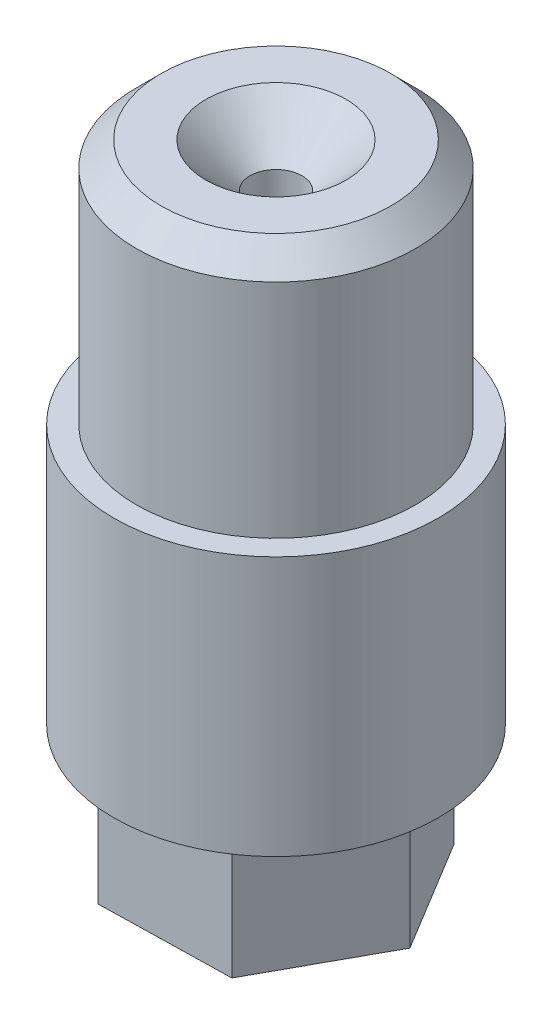
SolidWorks part; units mm, degrees
material "6061-T6 (SS)"
ref_plane "Front Plane" through (0, 0, 0) normal (0, 0, 1) x (1, 0, 0)
ref_plane "Top Plane" through (0, 0, 0) normal (0, 1, 0) x (1, 0, 0)
ref_plane "Right Plane" through (0, 0, 0) normal (1, 0, 0) x (0, 0, -1)
ref_axis "Axis1" through (0, 110.1512, 0) along (0, -1, 0)
sketch "Sketch1" plane through (0, 0, 0) normal (0, 0, 1) x (1, 0, 0)
  line L0 (-15.875, 25.4) -> (-13.6487, 25.4)
  line L1 (-15.875, 0) -> (-15.875, 25.4)
  line L2 (-13.6487, 25.4) -> (-13.6487, 49.53)
  line L3 (-13.6487, 49.53) -> (-6.858, 49.53)
  line L6 (-15.875, 0) -> (0, 0)
  line L8 (0, 110.1512) -> (0, -76.4241) construction
  line L9 (0, 42.672) -> (0, 0)
  line L10 (-6.858, 49.53) -> (0, 42.672)
  dimension "D1" = 15.875
  dimension "D2" = 25.4
  dimension "D3" = 135
  dimension "D4" = 6.858
  dimension "D5" = 13.6487
  dimension "D6" = 49.53
revolve "Revolve1" add sketch "Sketch1" angle 360 about axis through (0, 110.1512, 0) along (0, -1, 0)
cosmetic thread "Cosmetic Thread1" parameters "D2"=27.4295
ref_plane "Plane2" through (0, 110.1512, 0) normal (-1, 0, 0) x (0, 0, 1)
sketch "Sketch12" plane through (0, 0, 0) normal (0, -1, 0) x (1, 0, 0)
  line L1 (-12.8287, 0.2741) -> (-6.6517, -10.9729)
  line L2 (-6.6517, -10.9729) -> (6.177, -11.247)
  line L3 (6.177, -11.247) -> (12.8287, -0.2741)
  line L4 (12.8287, -0.2741) -> (6.6517, 10.9729)
  line L5 (6.6517, 10.9729) -> (-6.177, 11.247)
  line L6 (-6.177, 11.247) -> (-12.8287, 0.2741)
  circle A0 centre (0, 0) radius 11.1125 construction
  dimension "D1" = 22.225
extrude "Boss-Extrude2" add sketch "Sketch12" along normal blind 12.7
ref_plane "Plane4" through (0, 110.1512, 0) normal (-1, 0, 0) x (0, 0, 1)
ref_plane "Plane6" through (0, 110.1512, 0) normal (-1, 0, 0) x (0, 0, 1)
chamfer "Chamfer2" distance 2.413 1 edges at (0, 49.53, 13.6487)
thread "Thread1" pitch 3.6286 start angle 0, offset 0, length 0, pitch 3.6286, diameter 31.75
ref_plane "Plane7" through (-15.875, 50.8, 0) normal (0, 0, 1) x (-1, 0, 0)
sketch "Thread Profile1" plane through (-15.875, 50.8, 0) normal (0, 0, 1) x (-1, 0, 0)
  line L0 (0, 0) -> (0, 3.6286) construction
  line L11 (0, 0) -> (0, 3.175)
  line L12 (0, 3.175) -> (-1.964, 2.0411)
  line L13 (-1.964, 2.0411) -> (-1.964, 1.1339)
  line L15 (-1.964, 1.1339) -> (0, 0)
  line L17 (-1.964, 1.5875) -> (0, 1.5875) construction
  point P2 (0, 0)
  dimension "Pitch" = 3.6286
  dimension "Profile_Angle" = 60
  dimension "Profile_Land" = 0.9071
  dimension "Profile_Height" = 1.964
sketch "Sketch13" plane through (0, -12.7, 0) normal (0, -1, 0) x (1, 0, 0)
  circle A0 centre (0, 0) radius 2.54
  dimension "D1" = 5.08
extrude "Cut-Extrude1" cut sketch "Sketch13" against normal through all
